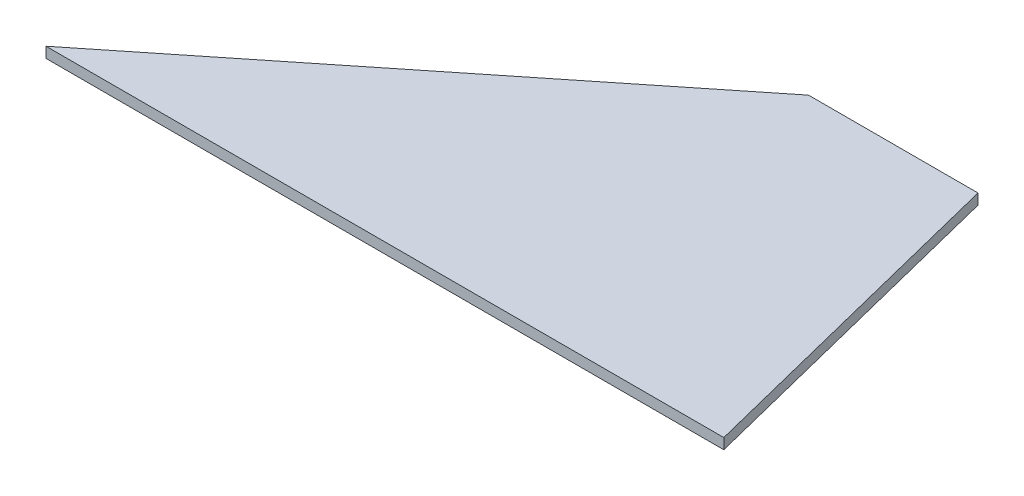
SolidWorks part; units mm, degrees
material "6063-T6"
ref_plane "Front Plane" through (0, 0, 0) normal (0, 0, 1) x (1, 0, 0)
ref_plane "Top Plane" through (0, 0, 0) normal (0, 1, 0) x (1, 0, 0)
ref_plane "Right Plane" through (0, 0, 0) normal (1, 0, 0) x (0, 0, -1)
sketch "Sketch1" plane through (0, 0, 0) normal (0, 1, 0) x (1, 0, 0)
  line L0 (0, 0) -> (-406.4, 0)
  line L1 (-406.4, 0) -> (-152.4, 203.2)
  line L2 (-152.4, 203.2) -> (-50.8, 203.2)
  line L3 (-50.8, 203.2) -> (0, 0)
  dimension "D1" = 406.4
  dimension "D2" = 101.6
  dimension "D3" = 254
  dimension "D4" = 203.2
extrude "Boss-Extrude1" add sketch "Sketch1" along normal blind 6.35
